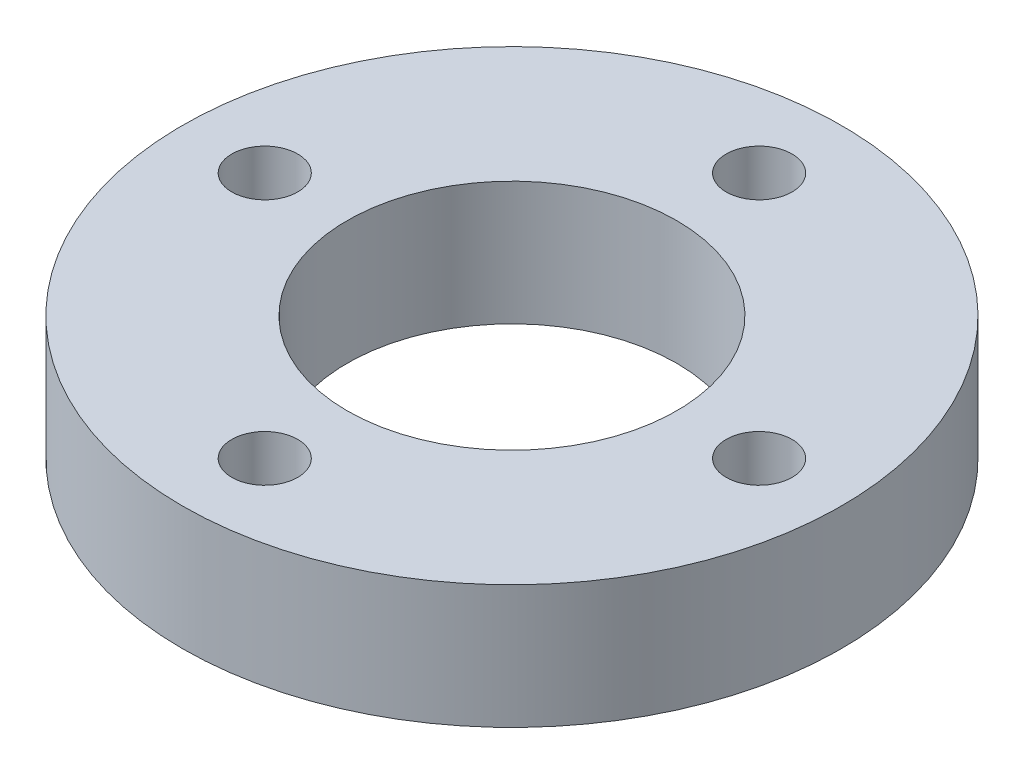
SolidWorks part; units mm, degrees
ref_plane "前视基准面" through (0, 0, 0) normal (0, 0, 1) x (1, 0, 0)
ref_plane "上视基准面" through (0, 0, 0) normal (0, 1, 0) x (1, 0, 0)
ref_plane "右视基准面" through (0, 0, 0) normal (1, 0, 0) x (0, 0, -1)
sketch "草图1" plane through (0, 0, 0) normal (0, 1, 0) x (1, 0, 0)
  circle A0 centre (0, 0) radius 8
  circle A1 centre (0, 0) radius 16
  circle A2 centre (-12, 0) radius 1.6
  circle A3 centre (0, 12) radius 1.6
  circle A4 centre (12, 0) radius 1.6
  circle A5 centre (0, -12) radius 1.6
  point P15 (0, 0)
  dimension "D1" = 16
  dimension "D2" = 32
  dimension "D3" = 3.2
  dimension "D4" = 12
  dimension "D5" = 4
extrude "凸台-拉伸1" add sketch "草图1" along normal blind 6
